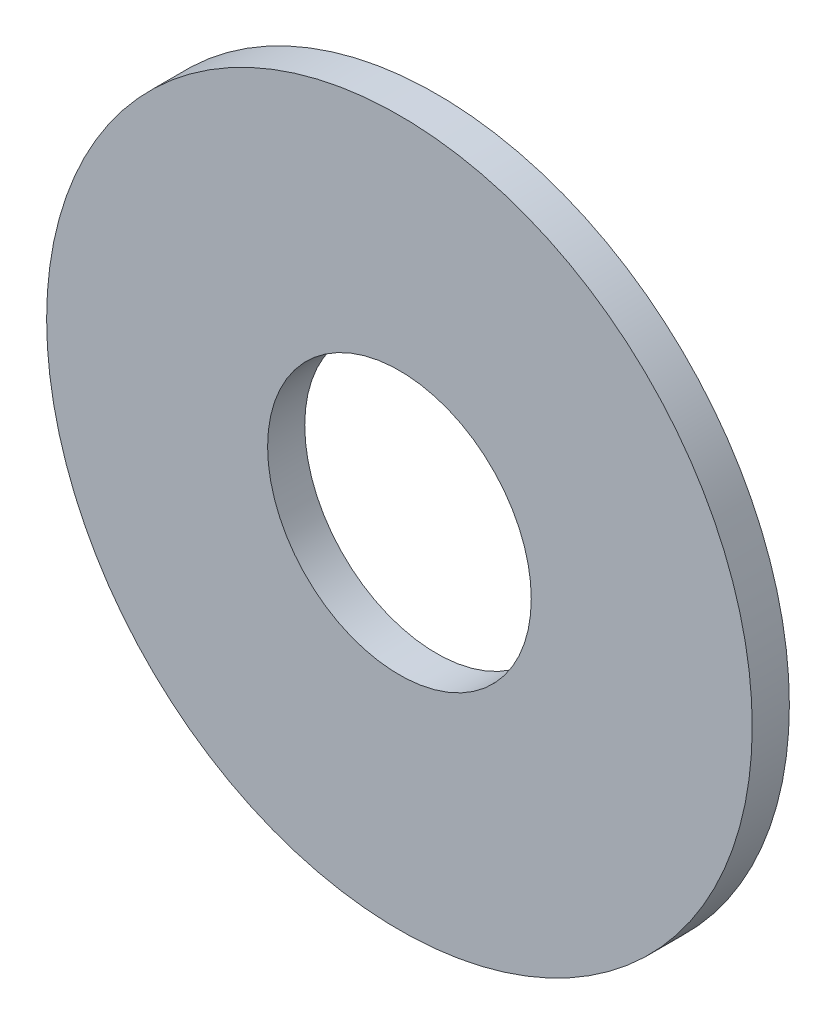
SolidWorks part; units mm, degrees
ref_plane "Ebene vorne" through (0, 0, 0) normal (0, 0, 1) x (1, 0, 0)
ref_plane "Ebene oben" through (0, 0, 0) normal (0, 1, 0) x (1, 0, 0)
ref_plane "Ebene rechts" through (0, 0, 0) normal (1, 0, 0) x (0, 0, -1)
sketch "Skizze1" plane through (0, 0, 0) normal (0, 0, 1) x (1, 0, 0)
  circle A0 centre (0, 0) radius 3.55
  circle A1 centre (0, 0) radius 9.5
  point P5 (0.136, 0)
  dimension "D1" = 19
  dimension "D2" = 7.1
extrude "Aufsatz-Linear austragen1" add sketch "Skizze1" along normal blind 1
